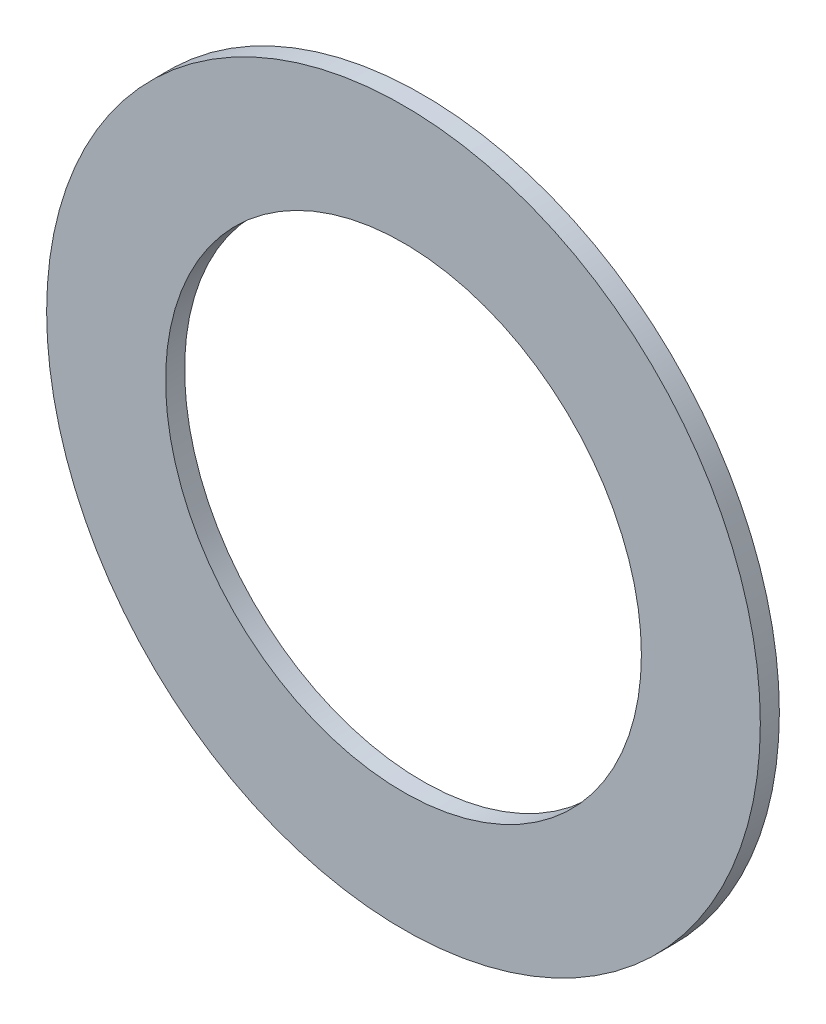
SolidWorks part; units mm, degrees
material "Wrought Stainless Steel"
ref_plane "Front Plane" through (0, 0, 0) normal (0, 0, 1) x (1, 0, 0)
ref_plane "Top Plane" through (0, 0, 0) normal (0, 1, 0) x (1, 0, 0)
ref_plane "Right Plane" through (0, 0, 0) normal (1, 0, 0) x (0, 0, -1)
sketch "Sketch1" plane through (0, 0, 0) normal (0, 0, 1) x (1, 0, 0)
  circle A0 centre (0, 0) radius 3.175
  circle A1 centre (0, 0) radius 4.7625
  dimension "D1" = 6.35
  dimension "D2" = 9.525
extrude "Boss-Extrude1" add sketch "Sketch1" along normal blind 0.254
